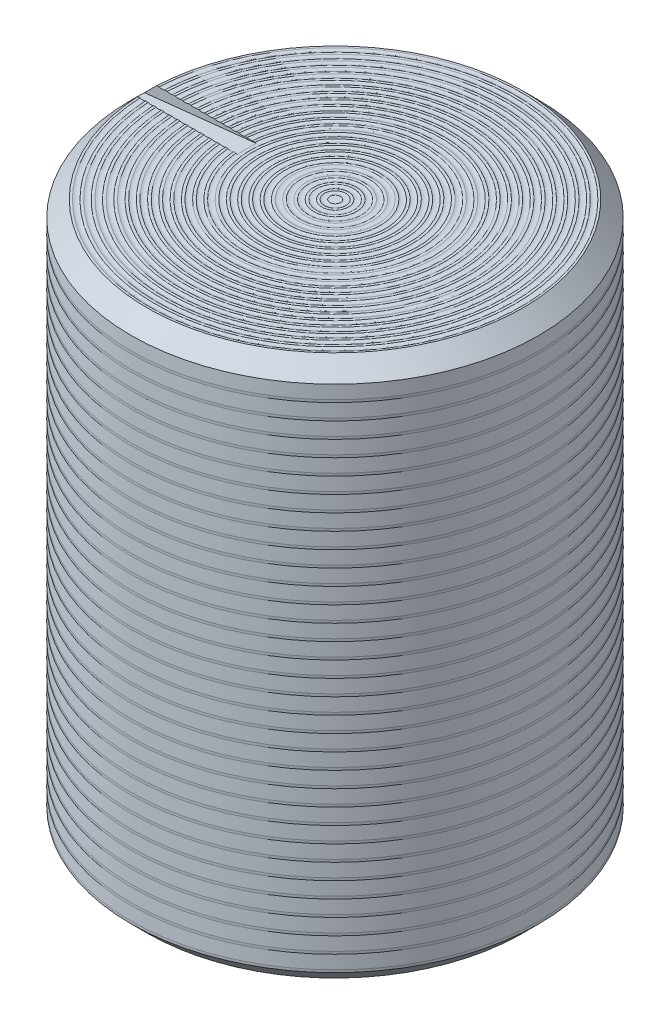
SolidWorks part; units mm, degrees
ref_plane "前视基准面" through (0, 0, 0) normal (0, 0, 1) x (1, 0, 0)
ref_plane "上视基准面" through (0, 0, 0) normal (0, 1, 0) x (1, 0, 0)
ref_plane "右视基准面" through (0, 0, 0) normal (1, 0, 0) x (0, 0, -1)
sketch "Sketch1" plane through (0, 0, 0) normal (0, 1, 0) x (1, 0, 0)
  circle A0 centre (0, 0) radius 6.4
extrude "Boss-Extrude1" add sketch "Sketch1" along normal blind 17
chamfer "Chamfer1" distance 0.5 angle 45 2 edges at (0, 0, 6.4) (0, 17, 6.4)
sketch "Sketch2" plane through (0, 0, 0) normal (0, 0, 1) x (1, 0, 0)
  line L0 (-6.4, 16.6) -> (-6.4, 17)
  line L1 (-6.4, 16.5) -> (-6.4, 0.5) construction
  line L2 (-6.4, 17) -> (-2.65, 17)
  line L3 (5.9, 17) -> (-5.9, 17) construction
  line L4 (-2.65, 17) -> (-6.4, 16.6)
extrude "Cut-Extrude1" cut sketch "Sketch2" against normal mid plane 0.6
sketch "Sketch3" plane through (0, 0, 0) normal (0, 0, 1) x (1, 0, 0)
  line L0 (0, 0) -> (0, 18.3832) construction
  line L1 (-5.9, 0) -> (-6.4, 0) construction
  line L2 (-6.4, 0) -> (-6.4, 0.5) construction
  line L3 (-6.4, 0.0786) -> (-6.3674, 0.5) construction
  line L4 (6.4, 0.5) -> (-6.4, 0.5) construction
  line L5 (-6.3674, 0.5) -> (-6.4, 0.5) construction
  line L6 (-6.4, 0.5) -> (-6.4, 0.0786) construction
  line L8 (-6.4, 0.5786) -> (-6.3674, 1)
  line L9 (-6.3674, 1) -> (-6.4, 1)
  line L10 (-6.4, 1) -> (-6.4, 0.5786)
  line L11 (-6.4, 1.0786) -> (-6.3674, 1.5)
  line L12 (-6.3674, 1.5) -> (-6.4, 1.5)
  line L13 (-6.4, 1.5) -> (-6.4, 1.0786)
  line L14 (-6.4, 1.5786) -> (-6.3674, 2)
  line L15 (-6.3674, 2) -> (-6.4, 2)
  line L16 (-6.4, 2) -> (-6.4, 1.5786)
  line L17 (-6.4, 2.0786) -> (-6.3674, 2.5)
  line L18 (-6.3674, 2.5) -> (-6.4, 2.5)
  line L19 (-6.4, 2.5) -> (-6.4, 2.0786)
  line L20 (-6.4, 2.5786) -> (-6.3674, 3)
  line L21 (-6.3674, 3) -> (-6.4, 3)
  line L22 (-6.4, 3) -> (-6.4, 2.5786)
  line L23 (-6.4, 3.0786) -> (-6.3674, 3.5)
  line L24 (-6.3674, 3.5) -> (-6.4, 3.5)
  line L25 (-6.4, 3.5) -> (-6.4, 3.0786)
  line L26 (-6.4, 3.5786) -> (-6.3674, 4)
  line L27 (-6.3674, 4) -> (-6.4, 4)
  line L28 (-6.4, 4) -> (-6.4, 3.5786)
  line L29 (-6.4, 4.0786) -> (-6.3674, 4.5)
  line L30 (-6.3674, 4.5) -> (-6.4, 4.5)
  line L31 (-6.4, 4.5) -> (-6.4, 4.0786)
  line L32 (-6.4, 4.5786) -> (-6.3674, 5)
  line L33 (-6.3674, 5) -> (-6.4, 5)
  line L34 (-6.4, 5) -> (-6.4, 4.5786)
  line L35 (-6.4, 5.0786) -> (-6.3674, 5.5)
  line L36 (-6.3674, 5.5) -> (-6.4, 5.5)
  line L37 (-6.4, 5.5) -> (-6.4, 5.0786)
  line L38 (-6.4, 5.5786) -> (-6.3674, 6)
  line L39 (-6.3674, 6) -> (-6.4, 6)
  line L40 (-6.4, 6) -> (-6.4, 5.5786)
  line L41 (-6.4, 6.0786) -> (-6.3674, 6.5)
  line L42 (-6.3674, 6.5) -> (-6.4, 6.5)
  line L43 (-6.4, 6.5) -> (-6.4, 6.0786)
  line L44 (-6.4, 6.5786) -> (-6.3674, 7)
  line L45 (-6.3674, 7) -> (-6.4, 7)
  line L46 (-6.4, 7) -> (-6.4, 6.5786)
  line L47 (-6.4, 7.0786) -> (-6.3674, 7.5)
  line L48 (-6.3674, 7.5) -> (-6.4, 7.5)
  line L49 (-6.4, 7.5) -> (-6.4, 7.0786)
  line L50 (-6.4, 7.5786) -> (-6.3674, 8)
  line L51 (-6.3674, 8) -> (-6.4, 8)
  line L52 (-6.4, 8) -> (-6.4, 7.5786)
  line L53 (-6.4, 8.0786) -> (-6.3674, 8.5)
  line L54 (-6.3674, 8.5) -> (-6.4, 8.5)
  line L55 (-6.4, 8.5) -> (-6.4, 8.0786)
  line L56 (-6.4, 8.5786) -> (-6.3674, 9)
  line L57 (-6.3674, 9) -> (-6.4, 9)
  line L58 (-6.4, 9) -> (-6.4, 8.5786)
  line L59 (-6.4, 9.0786) -> (-6.3674, 9.5)
  line L60 (-6.3674, 9.5) -> (-6.4, 9.5)
  line L61 (-6.4, 9.5) -> (-6.4, 9.0786)
  line L62 (-6.4, 9.5786) -> (-6.3674, 10)
  line L63 (-6.3674, 10) -> (-6.4, 10)
  line L64 (-6.4, 10) -> (-6.4, 9.5786)
  line L65 (-6.4, 10.0786) -> (-6.3674, 10.5)
  line L66 (-6.3674, 10.5) -> (-6.4, 10.5)
  line L67 (-6.4, 10.5) -> (-6.4, 10.0786)
  line L68 (-6.4, 10.5786) -> (-6.3674, 11)
  line L69 (-6.3674, 11) -> (-6.4, 11)
  line L70 (-6.4, 11) -> (-6.4, 10.5786)
  line L71 (-6.4, 11.0786) -> (-6.3674, 11.5)
  line L72 (-6.3674, 11.5) -> (-6.4, 11.5)
  line L73 (-6.4, 11.5) -> (-6.4, 11.0786)
  line L74 (-6.4, 11.5786) -> (-6.3674, 12)
  line L75 (-6.3674, 12) -> (-6.4, 12)
  line L76 (-6.4, 12) -> (-6.4, 11.5786)
  line L77 (-6.4, 12.0786) -> (-6.3674, 12.5)
  line L78 (-6.3674, 12.5) -> (-6.4, 12.5)
  line L79 (-6.4, 12.5) -> (-6.4, 12.0786)
  line L80 (-6.4, 12.5786) -> (-6.3674, 13)
  line L81 (-6.3674, 13) -> (-6.4, 13)
  line L82 (-6.4, 13) -> (-6.4, 12.5786)
  line L83 (-6.4, 13.0786) -> (-6.3674, 13.5)
  line L84 (-6.3674, 13.5) -> (-6.4, 13.5)
  line L85 (-6.4, 13.5) -> (-6.4, 13.0786)
  line L86 (-6.4, 13.5786) -> (-6.3674, 14)
  line L87 (-6.3674, 14) -> (-6.4, 14)
  line L88 (-6.4, 14) -> (-6.4, 13.5786)
  line L89 (-6.4, 14.0786) -> (-6.3674, 14.5)
  line L90 (-6.3674, 14.5) -> (-6.4, 14.5)
  line L91 (-6.4, 14.5) -> (-6.4, 14.0786)
  line L92 (-6.4, 14.5786) -> (-6.3674, 15)
  line L93 (-6.3674, 15) -> (-6.4, 15)
  line L94 (-6.4, 15) -> (-6.4, 14.5786)
  line L95 (-6.4, 15.0786) -> (-6.3674, 15.5)
  line L96 (-6.3674, 15.5) -> (-6.4, 15.5)
  line L97 (-6.4, 15.5) -> (-6.4, 15.0786)
  line L98 (-6.4, 15.5786) -> (-6.3674, 16)
  line L99 (-6.3674, 16) -> (-6.4, 16)
  line L100 (-6.4, 16) -> (-6.4, 15.5786)
  line L101 (-6.4, 16.0786) -> (-6.3674, 16.5)
  line L102 (-6.3674, 16.5) -> (-6.4, 16.5)
  line L103 (-6.4, 16.5) -> (-6.4, 16.0786)
  line L104 (-6.4, 16.5786) -> (-6.3674, 17)
  line L105 (-6.3674, 17) -> (-6.4, 17)
  line L106 (-6.4, 17) -> (-6.4, 16.5786)
  line L107 (-6.4, 17.0786) -> (-6.3674, 17.5)
  line L108 (-6.3674, 17.5) -> (-6.4, 17.5)
  line L109 (-6.4, 17.5) -> (-6.4, 17.0786)
  line L110 (-6.4, 0.0786) -> (-6.5133, 0.0786) construction
  point P12 (-6.3375, 0.5)
  point P114 (-6.3674, 0.5)
  dimension "D1" = 35
revolve "Cut-Revolve1" cut sketch "Sketch3" angle 360 about L0
sketch "Sketch4" plane through (0, 0, 0) normal (0, -1, 0) x (1, 0, 0)
  circle A0 centre (0, 0) radius 5.5
extrude "Cut-Extrude2" cut sketch "Sketch4" against normal blind 16.5
sketch "Sketch5" plane through (0, 0, 0) normal (0, 0, 1) x (1, 0, 0)
  line L0 (0.0038, 17) -> (0.0038, 18.6679) construction
  line L1 (5.9, 17) -> (-5.8924, 17) construction
  line L2 (0.0038, 17) -> (0.2538, 17) construction
  line L3 (0.2538, 17) -> (0.2538, 17.3034) construction
  line L4 (0.1696, 17) -> (0.338, 17)
  line L5 (0.4196, 17) -> (0.588, 17)
  line L6 (0.6696, 17) -> (0.838, 17)
  line L7 (0.9196, 17) -> (1.088, 17)
  line L8 (1.1696, 17) -> (1.338, 17)
  line L9 (1.4196, 17) -> (1.588, 17)
  line L10 (1.6696, 17) -> (1.838, 17)
  line L11 (1.9196, 17) -> (2.088, 17)
  line L12 (2.1696, 17) -> (2.338, 17)
  line L13 (2.4196, 17) -> (2.588, 17)
  line L14 (2.6696, 17) -> (2.838, 17)
  line L15 (2.9196, 17) -> (3.088, 17)
  line L16 (3.1696, 17) -> (3.338, 17)
  line L17 (3.4196, 17) -> (3.588, 17)
  line L18 (3.6696, 17) -> (3.838, 17)
  line L19 (3.9196, 17) -> (4.088, 17)
  line L20 (4.1696, 17) -> (4.338, 17)
  line L21 (4.4196, 17) -> (4.588, 17)
  line L22 (4.6696, 17) -> (4.838, 17)
  line L23 (4.9196, 17) -> (5.088, 17)
  line L24 (5.1696, 17) -> (5.338, 17)
  line L25 (5.4196, 17) -> (5.588, 17)
  line L26 (5.6696, 17) -> (5.838, 17)
  line L27 (5.9196, 17) -> (6.088, 17)
  line L28 (6.1696, 17) -> (6.338, 17)
  line L29 (6.4196, 17) -> (6.588, 17)
  line L30 (6.6696, 17) -> (6.838, 17)
  line L31 (6.9196, 17) -> (7.088, 17)
  line L32 (7.1696, 17) -> (7.338, 17)
  line L33 (7.4196, 17) -> (7.588, 17)
  spline S0 degree 2 poles (0.1696, 17) (0.2538, 16.9681) (0.338, 17) knots 0 0 0 1 1 1
  spline S1 degree 2 poles (0.4196, 17) (0.5038, 16.9681) (0.588, 17) knots 0 0 0 1 1 1
  spline S2 degree 2 poles (0.6696, 17) (0.7538, 16.9681) (0.838, 17) knots 0 0 0 1 1 1
  spline S3 degree 2 poles (0.9196, 17) (1.0038, 16.9681) (1.088, 17) knots 0 0 0 1 1 1
  spline S4 degree 2 poles (1.1696, 17) (1.2538, 16.9681) (1.338, 17) knots 0 0 0 1 1 1
  spline S5 degree 2 poles (1.4196, 17) (1.5038, 16.9681) (1.588, 17) knots 0 0 0 1 1 1
  spline S6 degree 2 poles (1.6696, 17) (1.7538, 16.9681) (1.838, 17) knots 0 0 0 1 1 1
  spline S7 degree 2 poles (1.9196, 17) (2.0038, 16.9681) (2.088, 17) knots 0 0 0 1 1 1
  spline S8 degree 2 poles (2.1696, 17) (2.2538, 16.9681) (2.338, 17) knots 0 0 0 1 1 1
  spline S9 degree 2 poles (2.4196, 17) (2.5038, 16.9681) (2.588, 17) knots 0 0 0 1 1 1
  spline S10 degree 2 poles (2.6696, 17) (2.7538, 16.9681) (2.838, 17) knots 0 0 0 1 1 1
  spline S11 degree 2 poles (2.9196, 17) (3.0038, 16.9681) (3.088, 17) knots 0 0 0 1 1 1
  spline S12 degree 2 poles (3.1696, 17) (3.2538, 16.9681) (3.338, 17) knots 0 0 0 1 1 1
  spline S13 degree 2 poles (3.4196, 17) (3.5038, 16.9681) (3.588, 17) knots 0 0 0 1 1 1
  spline S14 degree 2 poles (3.6696, 17) (3.7538, 16.9681) (3.838, 17) knots 0 0 0 1 1 1
  spline S15 degree 2 poles (3.9196, 17) (4.0038, 16.9681) (4.088, 17) knots 0 0 0 1 1 1
  spline S16 degree 2 poles (4.1696, 17) (4.2538, 16.9681) (4.338, 17) knots 0 0 0 1 1 1
  spline S17 degree 2 poles (4.4196, 17) (4.5038, 16.9681) (4.588, 17) knots 0 0 0 1 1 1
  spline S18 degree 2 poles (4.6696, 17) (4.7538, 16.9681) (4.838, 17) knots 0 0 0 1 1 1
  spline S19 degree 2 poles (4.9196, 17) (5.0038, 16.9681) (5.088, 17) knots 0 0 0 1 1 1
  spline S20 degree 2 poles (5.1696, 17) (5.2538, 16.9681) (5.338, 17) knots 0 0 0 1 1 1
  spline S21 degree 2 poles (5.4196, 17) (5.5038, 16.9681) (5.588, 17) knots 0 0 0 1 1 1
  spline S22 degree 2 poles (5.6696, 17) (5.7538, 16.9681) (5.838, 17) knots 0 0 0 1 1 1
  spline S23 degree 2 poles (5.9196, 17) (6.0038, 16.9681) (6.088, 17) knots 0 0 0 1 1 1
  spline S24 degree 2 poles (6.1696, 17) (6.2538, 16.9681) (6.338, 17) knots 0 0 0 1 1 1
  spline S25 degree 2 poles (6.4196, 17) (6.5038, 16.9681) (6.588, 17) knots 0 0 0 1 1 1
  spline S26 degree 2 poles (6.6696, 17) (6.7538, 16.9681) (6.838, 17) knots 0 0 0 1 1 1
  spline S27 degree 2 poles (6.9196, 17) (7.0038, 16.9681) (7.088, 17) knots 0 0 0 1 1 1
  spline S28 degree 2 poles (7.1696, 17) (7.2538, 16.9681) (7.338, 17) knots 0 0 0 1 1 1
  spline S29 degree 2 poles (7.4196, 17) (7.5038, 16.9681) (7.588, 17) knots 0 0 0 1 1 1
  point P9 (0.2538, 17)
  point P15 (0.5038, 17)
  point P19 (0.7538, 17)
  point P23 (1.0038, 17)
  point P27 (1.2538, 17)
  point P31 (1.5038, 17)
  point P35 (1.7538, 17)
  point P39 (2.0038, 17)
  point P43 (2.2538, 17)
  point P47 (2.5038, 17)
  point P51 (2.7538, 17)
  point P55 (3.0038, 17)
  point P59 (3.2538, 17)
  point P63 (3.5038, 17)
  point P67 (3.7538, 17)
  point P71 (4.0038, 17)
  point P75 (4.2538, 17)
  point P79 (4.5038, 17)
  point P83 (4.7538, 17)
  point P87 (5.0038, 17)
  point P91 (5.2538, 17)
  point P95 (5.5038, 17)
  point P99 (5.7538, 17)
  point P103 (6.0038, 17)
  point P107 (6.2538, 17)
  point P111 (6.5038, 17)
  point P115 (6.7538, 17)
  point P119 (7.0038, 17)
  point P123 (7.2538, 17)
  point P127 (7.5038, 17)
  dimension "D1" = 30
revolve "Cut-Revolve2" cut sketch "Sketch5" angle 360 about L0
